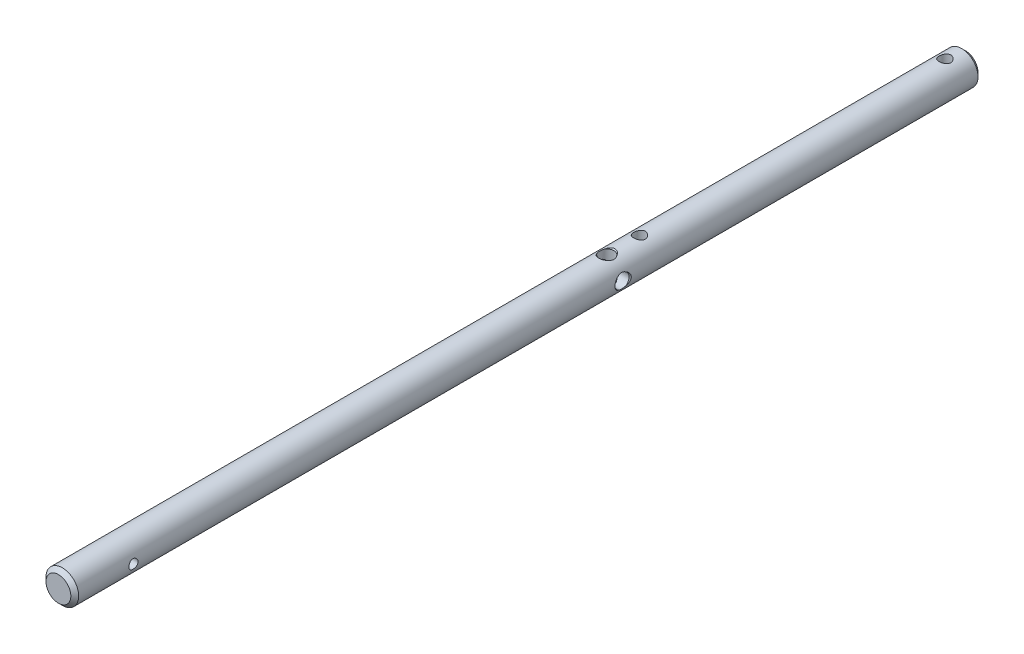
SolidWorks part; units mm, degrees
ref_plane "Front Plane" through (0, 0, 0) normal (0, 0, 1) x (1, 0, 0)
ref_plane "Top Plane" through (0, 0, 0) normal (0, 1, 0) x (1, 0, 0)
ref_plane "Right Plane" through (0, 0, 0) normal (1, 0, 0) x (0, 0, -1)
ref_plane "Plane1" through (0, 0, 0) normal (0, -1, 0) x (1, 0, 0)
sketch "Sketch1" plane through (0, 0, 0) normal (0, -1, 0) x (1, 0, 0)
  line L0 (3.175, 133.223) -> (0, 133.223)
  line L1 (0, 133.223) -> (0, 0)
  line L2 (0, 0) -> (3.175, 0)
  line L4 (3.175, 0) -> (3.175, 133.223)
  line L6 (0, 133.223) -> (0, 0) construction
  dimension "D1" = 3.175
  dimension "D2" = 133.223
revolve "Revolve1" add sketch "Sketch1" angle 360 about L6
ref_plane "Plane2" through (3.175, 0, 0) normal (1, 0, 0) x (0, 0, -1)
hole_wizard "#2-56 Tapped Hole1" positions "Sketch3" profile "Sketch2" tap size "#2-56" standard "ANSI Inch" end condition through all
sketch "Sketch3" plane through (3.175, 0, 0) normal (1, 0, 0) x (0, 0, -1)
  line L0 (-133.223, 3.175) -> (-133.223, -3.175) construction
  point P0 (-121.8018, 0)
  dimension "D1" = 11.4212
sketch "Sketch2" plane through (3.175, 0, 121.8018) normal (0, 1, 0) x (0, 0, -1)
  line L0 (0, 0) -> (0, 6.35)
  line L1 (0, 6.35) -> (0.889, 6.35)
  line L2 (0.889, 6.35) -> (0.889, 0)
  line L5 (0.889, 0) -> (0, 0)
  line L11 (0, -6.35) -> (0, 107.95) construction
  dimension "Thru Tap Drill Dia." = 1.778
  dimension "Thru Tap Drill Depth" = 6.35
cosmetic thread "Hole Thread1" parameters "D2"=2.1844
sketch "Sketch4" plane through (0, 0, 0) normal (0, 0, -1) x (-1, 0, 0)
  circle A1 centre (0, 0) radius 3.175
  circle A2 centre (0, 0) radius 3.175
  dimension "D1" = 0
extrude "Boss-Extrude1" add sketch "Sketch4" along normal blind 43.053
chamfer "Chamfer1" distance 0.762 angle 45 2 edges at (-3.175, 0, 133.223) (-3.175, 0, -43.053)
ref_plane "Plane3" through (0, -3.175, 0) normal (0, -1, 0) x (-1, 0, 0)
hole_wizard "#4-40 Tapped Hole2" positions "Sketch7" profile "Sketch8" tap size "#4-40" standard "ANSI Inch" end condition through all
sketch "Sketch7" plane through (0, -3.175, 0) normal (0, -1, 0) x (-1, 0, 0)
  line L0 (-2.413, -133.223) -> (2.413, -133.223) construction
  point P0 (0, -20.32)
  point P6 (0, 39.0271)
  dimension "D1" = 112.903
  dimension "D2" = 59.3471
sketch "Sketch8" plane through (0, -3.175, 20.32) normal (1, 0, 0) x (0, 0, -1)
  line L0 (0, 0) -> (0, 6.35)
  line L1 (0, 6.35) -> (1.1303, 6.35)
  line L2 (1.1303, 6.35) -> (1.1303, 0)
  line L5 (1.1303, 0) -> (0, 0)
  line L11 (0, -6.35) -> (0, 107.95) construction
  dimension "Thru Tap Drill Dia." = 2.2606
  dimension "Thru Tap Drill Depth" = 6.35
cosmetic thread "Hole Thread2" parameters "D2"=2.8448
cosmetic thread "Hole Thread3" parameters "D2"=2.8448
hole_wizard "7/64 (0.10938) Diameter Hole1" positions "Sketch9" profile "Sketch10" hole size "7/64" standard "ANSI Inch" end condition through all
sketch "Sketch9" plane through (0, -3.175, 0) normal (0, -1, 0) x (-1, 0, 0)
  circle A0 centre (0, -20.32) radius 1.1303 construction
  point P0 (0, -26.67)
  dimension "D1" = 6.35
sketch "Sketch10" plane through (0, -3.175, 26.67) normal (1, 0, 0) x (0, 0, -1)
  line L0 (0, 0) -> (0, 6.35)
  line L1 (0, 6.35) -> (1.5875, 6.35)
  line L2 (1.3891, 6.1218) -> (1.3891, 0)
  line L5 (1.3891, 0) -> (0, 0)
  line L7 (1.5875, 6.35) -> (1.3891, 6.1218)
  line L8 (-1.5875, 6.35) -> (-1.3891, 6.1218) construction
  line L11 (0, -6.35) -> (0, 107.95) construction
  dimension "Thru Hole Dia." = 2.7783
  dimension "Thru Hole Depth" = 6.35
  dimension "Far C'Sink Dia." = 3.175
  dimension "Far C'Sink Angle" = 82
hole_wizard "7/64 (0.10938) Diameter Hole2" positions "Sketch11" profile "Sketch13" hole size "7/64" standard "ANSI Inch" end condition through all
sketch "Sketch11" plane through (3.175, 0, 0) normal (1, 0, 0) x (0, 0, -1)
  point P0 (-26.67, 0)
sketch "Sketch13" plane through (3.175, 0, 26.67) normal (0, 1, 0) x (0, 0, -1)
  line L0 (0, 0) -> (0, 6.35)
  line L1 (0, 6.35) -> (1.3891, 6.35)
  line L2 (1.3891, 6.35) -> (1.3891, 0.2282)
  line L3 (1.3891, 0.2282) -> (1.5875, 0)
  line L5 (1.5875, 0) -> (0, 0)
  line L6 (-1.3891, 0.2282) -> (-1.5875, 0) construction
  line L11 (0, -6.35) -> (0, 107.95) construction
  dimension "Thru Hole Dia." = 2.7783
  dimension "Thru Hole Depth" = 6.35
  dimension "Near C'Sink Dia." = 3.175
  dimension "Near C'Sink Angle" = 82
